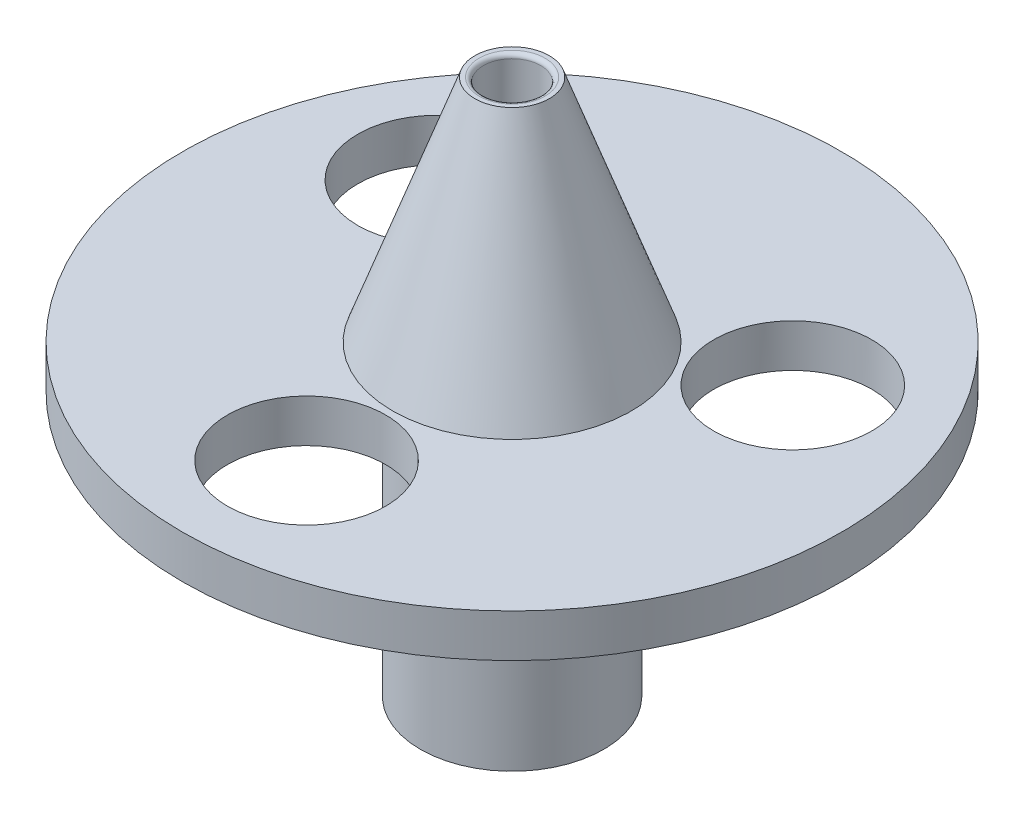
SolidWorks part; units mm, degrees
ref_plane "Front Plane" through (0, 0, 0) normal (0, 0, 1) x (1, 0, 0)
ref_plane "Top Plane" through (0, 0, 0) normal (0, 1, 0) x (1, 0, 0)
ref_plane "Right Plane" through (0, 0, 0) normal (1, 0, 0) x (0, 0, -1)
sketch "Sketch2" plane through (0, 0, 0) normal (0, 0, 1) x (1, 0, 0)
  line L0 (2, 0) -> (2.6, 0)
  line L2 (2, 0) -> (2, -16)
  line L3 (2, -16) -> (3.4, -16)
  line L4 (2.6, 0) -> (8.3409, -16)
  line L8 (3.4, -16) -> (3.4, -37.4278)
  line L9 (0, 0) -> (0, -37.4278) construction
  line L10 (6.4, -19) -> (6.4, -37.4278)
  line L12 (8.3409, -16) -> (20.3409, -16)
  line L13 (3.4, -37.4278) -> (6.4, -37.4278)
  line L14 (20.3409, -16) -> (20.3409, -19)
  line L15 (20.3409, -19) -> (6.4, -19)
revolve "Revolve1" add sketch "Sketch2" angle 360 about L9
fillet "Fillet1" radius 0.3 1 edges at (0, 0, 2)
sketch "Sketch3" plane through (0, -37.4278, 0) normal (0, -1, 0) x (1, 0, 0)
  circle A0 centre (0, 0) radius 3.6
extrude "Cut-Extrude1" cut sketch "Sketch3" along normal blind 1 and the other way blind 22
fillet "Fillet2" radius 0.5 1 edges at (0, -15.4278, -2)
fillet "Fillet3" radius 0.5 1 edges at (0, -37.4278, 3.6)
ref_plane "Plane2" through (0, -16, 0) normal (0, 1, 0) x (1, 0, 0)
ref_plane "Plane3" through (0, -19, 0) normal (0, -1, 0) x (-1, 0, 0)
sketch "Sketch5" plane through (0, -16, 0) normal (0, 1, 0) x (1, 0, 0)
  line L2 (-3.25, -14) -> (3.25, -14)
  line L3 (-3.25, -14) -> (-3.25, -16)
  line L4 (-3.25, -16) -> (3.25, -16)
  line L5 (3.25, -14) -> (3.25, -16)
sketch "Sketch6" plane through (0, -19, 0) normal (0, -1, 0) x (1, 0, 0)
  line L2 (4.25, 14) -> (-4.25, 14)
  line L3 (4.25, 14) -> (4.25, 16)
  line L4 (4.25, 16) -> (-4.25, 16)
  line L5 (-4.25, 14) -> (-4.25, 16)
loft "Cut-Loft2" cut profiles "Sketch5", "Sketch6"
sketch "Sketch7" plane through (0, -16, 0) normal (0, 1, 0) x (1, 0, 0)
  line L1 (-3.25, -13.5) -> (3.25, -13.5)
  line L2 (-3.25, -13.5) -> (-3.25, -16.5)
  line L3 (-3.25, -16.5) -> (3.25, -16.5)
  line L4 (3.25, -13.5) -> (3.25, -16.5)
sketch "Sketch8" plane through (0, -19, 0) normal (0, -1, 0) x (1, 0, 0)
  line L1 (4.25, 13.5) -> (-4.25, 13.5)
  line L2 (4.25, 13.5) -> (4.25, 16.5)
  line L3 (4.25, 16.5) -> (-4.25, 16.5)
  line L4 (-4.25, 13.5) -> (-4.25, 16.5)
loft "Cut-Loft3" cut profiles "Sketch8", "Sketch7"
sketch "Sketch11" plane through (0, -16, 0) normal (0, 1, 0) x (1, 0, 0)
  line L0 (0, 0) -> (-17.6157, 10.1705)
  line L1 (-17.6157, 10.1705) -> (-12.4196, 7.1705)
  circle A0 centre (0, 0) radius 20.3409 construction
  circle A1 centre (-12.4196, 7.1705) radius 5.52
  circle A2 centre (0, 14.3409) radius 5.52
  circle A3 centre (12.4196, 7.1705) radius 5.52
  point P13 (0, 0)
  dimension "D1" = 3
extrude "Cut-Extrude3" cut sketch "Sketch11" against normal blind 10 contours A2 | A3 | L0 A1 | L0 A1
sketch "Sketch13" plane through (0, -16, 0) normal (0, 1, 0) x (1, 0, 0)
  line L0 (-8.3409, 0) -> (-20.3409, 0)
  line L1 (8.3409, 0) -> (20.3409, 0)
  line L2 (-10.1705, -17.6157) -> (-4.1705, -7.2234)
  line L3 (9.9324, -17.7511) -> (4.0728, -7.2789)
  circle A0 centre (0, 0) radius 20.3409 construction
  arc A1 (20.3409, 0) -> (9.9324, -17.7511) centre (0, 0) cw
  arc A2 (-20.3409, 0) -> (-10.1705, -17.6157) centre (0, 0) ccw
  circle A3 centre (0, 0) radius 8.3409 construction
  arc A4 (-4.1705, -7.2234) -> (-8.3409, 0) centre (0, 0) cw
  arc A5 (4.0728, -7.2789) -> (8.3409, 0) centre (0, 0) ccw
extrude "Cut-Extrude4" cut sketch "Sketch13" against normal blind 10
sketch "Sketch14" plane through (0, -16, 0) normal (0, 1, 0) x (1, 0, 0)
  line L0 (0, 0) -> (23, 0)
  line L1 (0, 0) -> (-23, 0)
  line L2 (0, 0) -> (0, 23)
  line L3 (0, 0) -> (-20.17, 0)
  line L4 (0, 0) -> (20.17, 0)
  line L5 (0, 0) -> (0, 20.17)
  arc A0 (23, 0) -> (-23, 0) centre (0, 0) ccw
  arc A1 (-20.17, 0) -> (20.17, 0) centre (0, 0) cw
  arc M7 (20.3409, 0) -> (-20.3409, 0) centre (0, 0) ccw
extrude "Boss-Extrude1" add sketch "Sketch14" against normal blind 3 contours L0 A0 L2 M7 | L2 A0 L1 M7
sketch "Sketch15" plane through (0, -16, 0) normal (0, 1, 0) x (1, 0, 0)
  circle A0 centre (0, 0) radius 23
  circle A1 centre (0, 0) radius 8.3409
  circle A2 centre (-12.4196, 7.1705) radius 5.6
  circle A3 centre (12.4196, 7.1705) radius 5.6
  circle A4 centre (0, -14.3409) radius 5.6
  point P14 (0, 0)
  dimension "D1" = 3
extrude "Boss-Extrude4" add sketch "Sketch15" against normal blind 3
sketch "Sketch16" plane through (0, -16, 0) normal (0, 1, 0) x (1, 0, 0)
  line L0 (0, 0) -> (12.4196, 7.1705)
  line L1 (0, 0) -> (0, -14.3409)
  circle A0 centre (12.4196, 7.1705) radius 5.52
  circle A1 centre (0, -14.3409) radius 5.52
  point P6 (10.9371, 12.4877)
extrude "Cut-Extrude6" cut sketch "Sketch16" against normal blind 3
